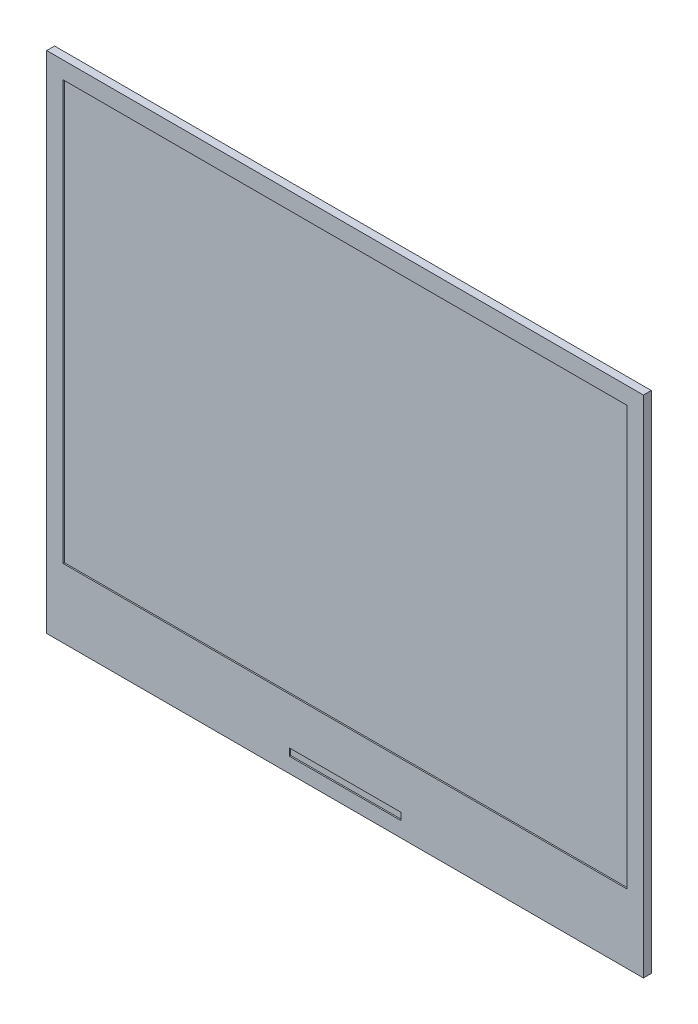
SolidWorks part; units mm, degrees
material "Plastique personnalisé"
ref_plane "Plan de face" through (0, 0, 0) normal (0, 0, 1) x (1, 0, 0)
ref_plane "Plan de dessus" through (0, 0, 0) normal (0, 1, 0) x (1, 0, 0)
ref_plane "Plan de droite" through (0, 0, 0) normal (1, 0, 0) x (0, 0, -1)
sketch "Esquisse1" plane through (0, 0, 0) normal (0, 0, 1) x (1, 0, 0)
  line L1 (0, 0) -> (91, 0)
  line L2 (0, 0) -> (0, 77)
  line L3 (0, 77) -> (91, 77)
  line L4 (91, 0) -> (91, 77)
  dimension "D1" = 91
  dimension "D2" = 77
extrude "Boss.-Extru.1" add sketch "Esquisse1" along normal blind 1.2
sketch "Esquisse2" plane through (0, 0, 1.2) normal (0, 0, 1) x (1, 0, 0)
  line L0 (0, 77) -> (0, 74.5046) construction
  line L1 (0, 77) -> (0, 0) construction
  line L2 (0, 74.5046) -> (91, 74.5046) construction
  line L3 (91, 0) -> (91, 77) construction
  line L4 (91, 74.5046) -> (88.4965, 74.5046) construction
  line L5 (88.4965, 74.5046) -> (88.4965, 0) construction
  line L6 (0, 0) -> (91, 0) construction
  line L7 (88.4965, 0) -> (88.4965, 10.5026) construction
  line L8 (88.4965, 10.5026) -> (0, 10.5026) construction
  line L9 (0, 10.5026) -> (2.4998, 10.5026) construction
  line L10 (2.4998, 10.5026) -> (2.4998, 74.5046) construction
  line L12 (2.4998, 74.3899) -> (88.4965, 74.3899)
  line L13 (2.4998, 74.3899) -> (2.4998, 10.5026)
  line L14 (2.4998, 10.5026) -> (88.4965, 10.5026)
  line L15 (88.4965, 74.3899) -> (88.4965, 10.5026)
extrude "Enlèv. mat.-Extru.1" cut sketch "Esquisse2" against normal blind 0.2
sketch "Esquisse3" plane through (0, 0, 1.2) normal (0, 0, 1) x (1, 0, 0)
  line L0 (0, 0) -> (36.9961, 0) construction
  line L1 (0, 0) -> (91, 0) construction
  line L2 (36.9961, 0) -> (36.9961, 2.2975) construction
  line L3 (91, 0) -> (53.997, 0) construction
  line L4 (53.997, 0) -> (53.997, 2.2975) construction
  line L5 (53.997, 2.2975) -> (36.9961, 2.2975) construction
  line L7 (36.9961, 2.2975) -> (53.997, 2.2975)
  line L8 (36.9961, 2.2975) -> (36.9961, 3.3991)
  line L9 (36.9961, 3.3991) -> (53.997, 3.3991)
  line L10 (53.997, 2.2975) -> (53.997, 3.3991)
extrude "Enlèv. mat.-Extru.2" cut sketch "Esquisse3" against normal blind 0.2
